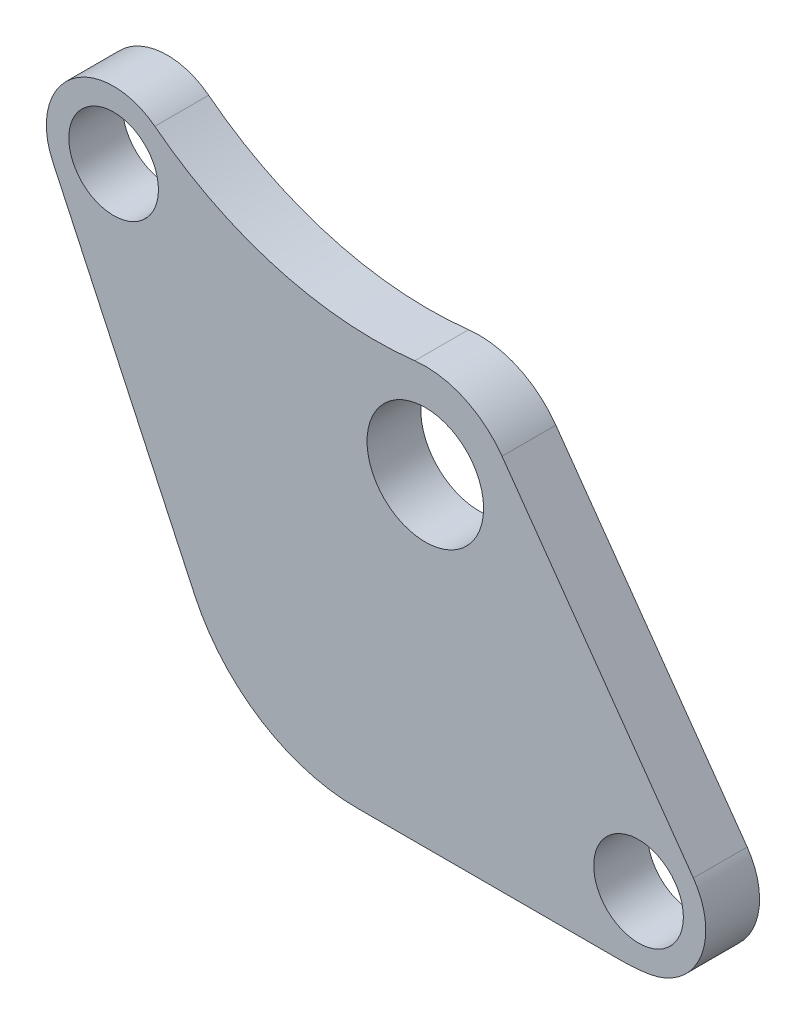
SolidWorks part; units mm, degrees
ref_plane "Front Plane" through (0, 0, 0) normal (0, 0, 1) x (1, 0, 0)
ref_plane "Top Plane" through (0, 0, 0) normal (0, 1, 0) x (1, 0, 0)
ref_plane "Right Plane" through (0, 0, 0) normal (1, 0, 0) x (0, 0, -1)
sketch "Sketch1" plane through (0, 0, 0) normal (0, 0, 1) x (1, 0, 0)
  line L0 (0, 0) -> (12.5, 0) construction
  line L1 (-3.2476, -1.875) -> (0, -3.75) construction
  line L2 (0, -3.75) -> (3.2476, -1.875) construction
  line L3 (3.2476, -1.875) -> (3.2476, 1.875) construction
  line L4 (3.2476, 1.875) -> (0, 3.75) construction
  line L5 (0, 3.75) -> (-3.2476, 1.875) construction
  line L6 (-3.2476, 1.875) -> (-3.2476, -1.875) construction
  line L7 (0, 0) -> (11.8916, -14.1718) construction
  line L9 (-17.3843, 6.3274) -> (0, 0) construction
  line L10 (-16.3063, -18) -> (25.6953, -18) construction
  line L12 (-10.1779, -18) -> (10.9061, -18)
  line L13 (4.2798, 3.0366) -> (14.9499, -12.0018)
  line L14 (-20.783, 4.7426) -> (-10.1779, -18)
  line L15 (0, 0) -> (0, -18) construction
  circle A0 centre (0, 0) radius 12.5 construction
  circle A1 centre (0, 0) radius 3.75 construction
  circle A2 centre (0, 0) radius 5.2476 construction
  circle A3 centre (0, 0) radius 3.2476 construction
  circle A4 centre (-17.3843, 6.3274) radius 2.5
  circle A5 centre (11.8916, -14.1718) radius 2.5
  circle A6 centre (-17.3843, 6.3274) radius 6 construction
  circle A7 centre (11.8916, -14.1718) radius 6 construction
  circle A8 centre (0, 0) radius 3.3476 construction
  circle A9 centre (-17.3843, 6.3274) radius 3.75 construction
  circle A10 centre (11.8916, -14.1718) radius 3.75 construction
  arc A11 (10.9061, -18) -> (12.4828, -17.8749) centre (10.9061, -8) ccw
  arc A12 (-15.0851, 9.2898) -> (-0.5866, 5.2147) centre (-2.8224, 25.0893) ccw
  arc A13 (-15.0851, 9.2898) -> (-20.783, 4.7426) centre (-17.3843, 6.3274) ccw
  arc A14 (-0.5866, 5.2147) -> (4.2798, 3.0366) centre (0, 0) cw
  arc A15 (12.4828, -17.8749) -> (14.9499, -12.0018) centre (11.8916, -14.1718) ccw
  circle A16 centre (0, 0) radius 3.25
  dimension "D1" = 25
  dimension "D2" = 7.5
  dimension "D3" = 2
  dimension "D4" = 5
  dimension "D7" = 12
  dimension "D9" = 7.5
  dimension "D11" = 20
  dimension "D12" = 10
  dimension "D14" = 6.5
  dimension "D5" = 50
  dimension "D6" = 20
  dimension "D10" = 18
  dimension "D13" = 65
  dimension "D8" = 0.1
extrude "Boss-Extrude1" add sketch "Sketch1" along normal blind 3
fillet "Fillet1" radius 10 1 edges at (-10.1779, -18, 1.5)
